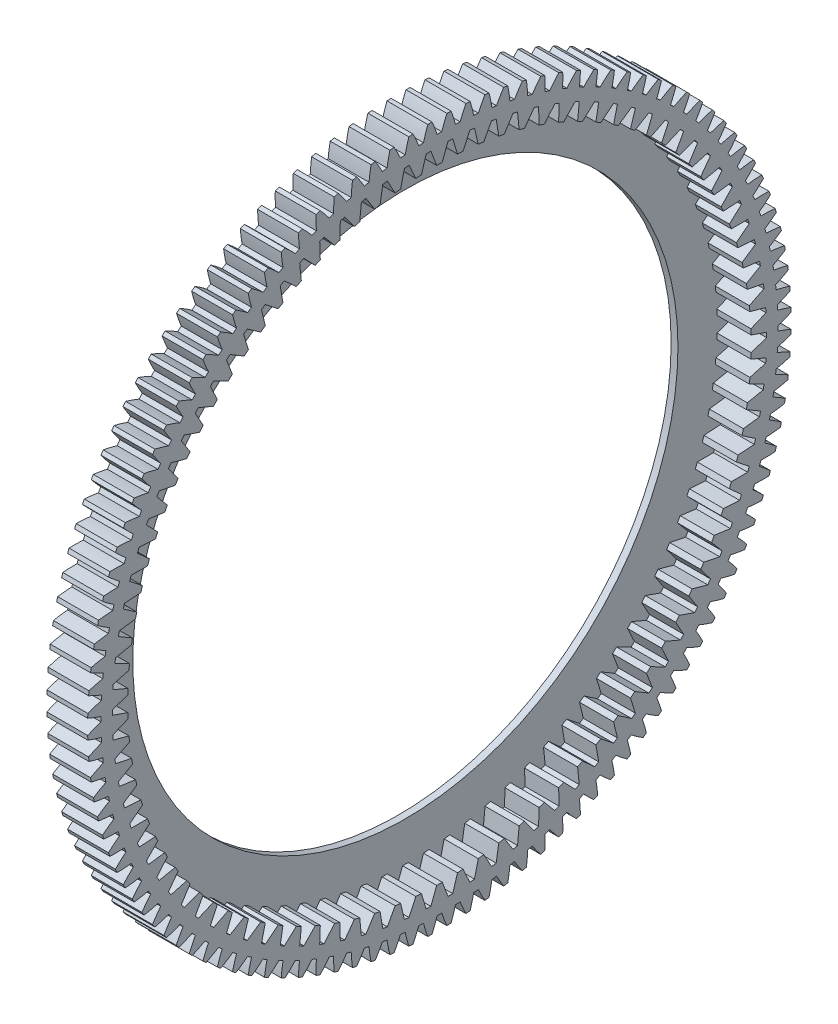
SolidWorks part; units mm, degrees
ref_plane "Plane1" through (0, 0, 0) normal (0, 0, 1) x (1, 0, 0)
ref_plane "Plane2" through (0, 0, 0) normal (0, 1, 0) x (1, 0, 0)
ref_plane "Plane3" through (0, 0, 0) normal (1, 0, 0) x (0, 0, -1)
sketch "HoldingSke" plane through (0, 0, 0) normal (0, 1, 0) x (1, 0, 0)
  line L0 (0, 0) -> (-0.2505, -0.5136)
  line L1 (-15, 0) -> (100, 0) construction
  line L2 (0, 0) -> (-2.1039, 2.3779)
  line L3 (0, 0) -> (-11.863, 4.5341)
  line L4 (0, 0) -> (-3.7858, 7.762)
  line L5 (0, 0) -> (-46.8476, -17.4728)
  line L6 (0, 0) -> (-9.9476, -6.7116)
  line L7 (-2.1039, 2.3779) -> (8.6586, 51.2059)
  line L8 (-76.2, 54.61) -> (-75.5, 54.61)
  line L9 (-71.009, 38.7566) -> (-53.1078, 45.2721)
  line L10 (-76.2, 71.12) -> (104.1128, 71.12)
  line L11 (0, 0) -> (-12, 0)
  line L12 (-76.2, 101.6) -> (-76.147, 101.6)
  line L13 (24.9733, 27.94) -> (52.9518, 28.4284)
  line L14 (24.9733, 27.94) -> (24.9743, 27.94)
  line L15 (24.9733, 27.94) -> (100.4006, 29.5858)
  line L16 (-63.627, -1.75) -> (-12.827, -1.75)
  circle A0 centre (0, 0) radius 2
  circle A1 centre (0, 0) radius 37.5
  circle A2 centre (0, 0) radius 37.5
  circle A3 centre (0, 0) radius 2
  dimension "MHD" = 75
  dimension "Hub_dia" = 75
  dimension "Bore" = 4
  dimension "MBD" = 4
  dimension "Num_teeth" = 116
  dimension "Pitch" = 0.5714
  dimension "Overall_len" = 50
  dimension "Show_teeth" = 116
  dimension "Thickness" = 12
  dimension "OAL" = 50.0001
  dimension "T_dim" = 0.7
  dimension "Ap" = 20
  dimension "H" = 19.05
  dimension "Pitch_radius" = 180.3128
  dimension "Width" = 12
  dimension "Backlash" = 0.053
  dimension "Addendum_fac" = 1
  dimension "Dedendum_fac" = 1.25
  dimension "Clearance_fac" = 0.25
  dimension "Dedendum_add" = 0.001
  dimension "Module" = 1.75
sketch "BasProSke" plane through (0, 0, 0) normal (0, 1, 0) x (1, 0, 0)
  line L0 (-10, 0) -> (60, 0) construction
  line L1 (0, 0) -> (0, 103.25)
  line L2 (0, 0) -> (12, 0)
  line L3 (12, 0) -> (12, 103.25)
  line L4 (12, 103.25) -> (0, 103.25)
  dimension "Thickness" = 12
  dimension "Diameter" = 206.5
revolve "Base-Revolve" add sketch "BasProSke" angle 360 about L0
sketch "TooCutSke" plane through (0, 0, 0) normal (1, 0, 0) x (0, 0, -1)
  line L1 (0, 0) -> (0, 107) construction
  line L2 (0, 0) -> (-1.4672, 101.4894) construction
  line L3 (0, 0) -> (-5.4967, 202.9094) construction
  line L4 (-1.4672, 101.4894) -> (-2.7483, 101.4547) construction
  arc A0 (0.6971, 99.3091) -> (-0.6971, 99.3091) centre (0, 0) ccw
  arc A1 (2.1948, 103.2521) -> (-2.1948, 103.2521) centre (0, 0) ccw
  circle A2 centre (0, 0) radius 101.5 construction
  circle A3 centre (0, 0) radius 95.3788 construction
  arc A4 (-0.6971, 99.3091) -> (-2.1948, 103.2521) centre (-39.349, 86.8837) ccw
  arc A5 (2.1948, 103.2521) -> (0.6971, 99.3091) centre (39.349, 86.8837) ccw
  dimension "Root_dia" = 198.623
  dimension "Overcut_dia" = 206.5508
  dimension "Pitch_dia" = 203
  dimension "Base_dia" = 190.7576
  dimension "Flank_rad" = 40.6
  dimension "Half_ang" = 1.552
  dimension "Half_CT" = 1.2817
extrude "ToothCut" cut sketch "TooCutSke" along normal through all
fillet "Breaks" [suppressed] radius 0.035
fillet "RootFillets" [suppressed] radius 0.4385
pattern_circular "TeethCuts" count 116 every 3.103 about axis through (-10, 0, 0) along (1, 0, 0) of "ToothCut", "RootFillets", "Breaks"
sketch "HubNeaOneSke" plane through (0, 0, 0) normal (-1, 0, 0) x (0, 0, 1)
  circle A0 centre (0, 0) radius 37.5
  dimension "Diameter" = 75
extrude "HubNearOne" [suppressed] add sketch "HubNeaOneSke" along normal blind 38.0001
sketch "HubNeaBotSke" plane through (0, 0, 0) normal (-1, 0, 0) x (0, 0, 1)
  circle A0 centre (0, 0) radius 37.5
  dimension "Diameter" = 75
extrude "HubNearBoth" [suppressed] add sketch "HubNeaBotSke" along normal blind 19
ref_plane "FarPln" through (12, 0, 0) normal (1, 0, 0) x (0, 0, -1)
sketch "HubFarSke" plane through (12, 0, 0) normal (1, 0, 0) x (0, 0, -1)
  circle A0 centre (0, 0) radius 37.5
  dimension "Diameter" = 75
extrude "HubFar" [suppressed] add sketch "HubFarSke" along normal blind 19
sketch "BorSke" plane through (0, 0, 0) normal (1, 0, 0) x (0, 0, -1)
  circle A0 centre (0, 0) radius 2
  dimension "Diameter" = 4
extrude "Bore" cut sketch "BorSke" along normal mid plane 100.0001
sketch "KeySke" plane through (0, 0, 0) normal (1, 0, 0) x (0, 0, -1)
  line L0 (-0.8, 0) -> (-0.8, 2.7)
  line L1 (-0.8, 2.7) -> (0.8, 2.7)
  line L2 (0.8, 2.7) -> (0.8, 0)
  line L3 (0, 0) -> (0, 34) construction
  line L4 (-0.8, 0) -> (0.8, 0)
  dimension "Offset" = 2.7
  dimension "Width" = 1.6
extrude "Keyway" [suppressed] cut sketch "KeySke" along normal mid plane 100.0001
pattern_circular "Keyway2" [suppressed] count 2 every 90 about axis through (-10, 0, 0) along (1, 0, 0)
sketch "Sketch1" plane through (12, 0, 0) normal (1, 0, 0) x (0, 0, -1)
  line L0 (3.8893, 95.9212) -> (5.2957, 91.3456)
  line L1 (2.5262, 95.9668) -> (0.8174, 91.4953)
  line L2 (8.9304, 95.5837) -> (6.9267, 91.2364)
  line L3 (10.2875, 95.4472) -> (11.3851, 90.7879)
  line L4 (15.2948, 94.7738) -> (13.0052, 90.57)
  line L5 (16.6397, 94.5469) -> (17.4236, 89.8247)
  line L6 (21.5908, 93.5406) -> (19.0256, 89.4991)
  line L7 (22.9175, 93.2244) -> (23.3843, 88.4604)
  line L8 (27.7904, 91.8896) -> (24.961, 88.0285)
  line L9 (29.0931, 91.4855) -> (29.2406, 86.7009)
  line L10 (33.8659, 89.8282) -> (30.7849, 86.1647)
  line L11 (35.1387, 89.338) -> (34.9663, 84.5543)
  line L12 (39.7901, 87.3656) -> (36.4713, 83.9161)
  line L13 (41.0273, 86.7915) -> (40.5358, 82.03)
  line L14 (45.5366, 84.5128) -> (41.9948, 81.2927)
  line L15 (46.7327, 83.8573) -> (45.9243, 79.1393)
  line L16 (51.0798, 81.2826) -> (47.3308, 78.3062)
  line L17 (52.2294, 80.5487) -> (51.1077, 75.8951)
  line L18 (56.3948, 77.6893) -> (52.4554, 74.97)
  line L19 (57.4928, 76.8803) -> (56.0628, 72.3121)
  line L20 (61.4579, 73.749) -> (57.3457, 71.2989)
  line L21 (62.4995, 72.8685) -> (60.7675, 68.406)
  line L22 (66.2466, 69.4794) -> (61.9799, 67.3094)
  line L23 (67.227, 68.5312) -> (65.2008, 64.1944)
  line L24 (70.7394, 64.8995) -> (66.3372, 63.0193)
  line L25 (71.6542, 63.8879) -> (69.3429, 59.6961)
  line L26 (74.9162, 60.0297) -> (70.3983, 58.4478)
  line L27 (75.7615, 58.9593) -> (73.1753, 54.9312)
  line L28 (78.7584, 54.8918) -> (74.145, 53.6152)
  line L29 (79.5303, 53.7673) -> (76.6809, 49.921)
  line L30 (82.2489, 49.5087) -> (77.5605, 48.5431)
  line L31 (82.944, 48.3352) -> (79.844, 44.6878)
  line L32 (85.3721, 43.9045) -> (80.6296, 43.2542)
  line L33 (85.9872, 42.6872) -> (82.6505, 39.255)
  line L34 (88.1139, 38.1043) -> (83.3387, 37.7722)
  line L35 (88.6464, 36.8486) -> (85.0879, 33.6469)
  line L36 (90.4622, 32.1338) -> (85.6755, 32.1214)
  line L37 (90.9096, 30.8454) -> (87.1453, 27.8885)
  line L38 (92.4065, 26.0198) -> (87.6296, 26.3272)
  line L39 (92.7669, 24.7044) -> (88.8134, 22.0056)
  line L40 (93.9381, 19.7897) -> (89.1924, 20.4154)
  line L41 (94.2098, 18.4531) -> (90.0849, 16.0243)
  line L42 (95.0501, 13.4711) -> (90.3568, 14.4124)
  line L43 (95.2319, 12.1194) -> (90.954, 9.9715)
  line L44 (95.7377, 7.0924) -> (91.1177, 8.345)
  line L45 (95.8288, 5.7315) -> (91.4169, 3.8742)
  line L46 (95.9976, 0.682) -> (91.4716, 2.2404)
  line L47 (95.9976, -0.682) -> (91.4716, -2.2404)
  line L48 (95.8288, -5.7315) -> (91.4169, -3.8742)
  line L49 (95.7377, -7.0924) -> (91.1177, -8.345)
  line L50 (95.2319, -12.1194) -> (90.954, -9.9715)
  line L51 (95.0501, -13.4711) -> (90.3568, -14.4124)
  line L52 (94.2098, -18.4531) -> (90.0849, -16.0243)
  line L53 (93.9381, -19.7897) -> (89.1924, -20.4154)
  line L54 (92.7669, -24.7044) -> (88.8134, -22.0056)
  line L55 (92.4065, -26.0198) -> (87.6296, -26.3272)
  line L56 (90.9096, -30.8454) -> (87.1453, -27.8885)
  line L57 (90.4622, -32.1338) -> (85.6755, -32.1214)
  line L58 (88.6464, -36.8486) -> (85.0879, -33.6469)
  line L59 (88.1139, -38.1043) -> (83.3387, -37.7722)
  line L60 (85.9872, -42.6872) -> (82.6505, -39.255)
  line L61 (85.3721, -43.9045) -> (80.6296, -43.2542)
  line L62 (82.944, -48.3352) -> (79.844, -44.6878)
  line L63 (82.2489, -49.5087) -> (77.5605, -48.5431)
  line L64 (79.5303, -53.7673) -> (76.6809, -49.921)
  line L65 (78.7584, -54.8918) -> (74.145, -53.6152)
  line L66 (75.7615, -58.9593) -> (73.1753, -54.9312)
  line L67 (74.9162, -60.0297) -> (70.3983, -58.4478)
  line L68 (71.6542, -63.8879) -> (69.3429, -59.6961)
  line L69 (70.7394, -64.8995) -> (66.3372, -63.0193)
  line L70 (67.227, -68.5312) -> (65.2008, -64.1944)
  line L71 (66.2466, -69.4794) -> (61.9799, -67.3094)
  line L72 (62.4995, -72.8685) -> (60.7675, -68.406)
  line L73 (61.4579, -73.749) -> (57.3457, -71.2989)
  line L74 (57.4928, -76.8803) -> (56.0628, -72.3121)
  line L75 (56.3948, -77.6893) -> (52.4554, -74.97)
  line L76 (52.2294, -80.5487) -> (51.1077, -75.8951)
  line L77 (51.0798, -81.2826) -> (47.3308, -78.3062)
  line L78 (46.7327, -83.8573) -> (45.9243, -79.1393)
  line L79 (45.5366, -84.5128) -> (41.9948, -81.2927)
  line L80 (41.0273, -86.7915) -> (40.5358, -82.03)
  line L81 (39.7901, -87.3656) -> (36.4713, -83.9161)
  line L82 (35.1387, -89.338) -> (34.9663, -84.5543)
  line L83 (33.8659, -89.8282) -> (30.7849, -86.1647)
  line L84 (29.0931, -91.4855) -> (29.2406, -86.7009)
  line L85 (27.7904, -91.8896) -> (24.961, -88.0285)
  line L86 (22.9175, -93.2244) -> (23.3843, -88.4604)
  line L87 (21.5908, -93.5406) -> (19.0256, -89.4991)
  line L88 (16.6397, -94.5469) -> (17.4236, -89.8247)
  line L89 (15.2948, -94.7738) -> (13.0052, -90.57)
  line L90 (10.2875, -95.4472) -> (11.3851, -90.7879)
  line L91 (8.9304, -95.5837) -> (6.9267, -91.2364)
  line L92 (3.8893, -95.9212) -> (5.2957, -91.3456)
  line L93 (2.5262, -95.9668) -> (0.8174, -91.4953)
  line L94 (-2.5262, -95.9668) -> (-0.8174, -91.4953)
  line L95 (-3.8893, -95.9212) -> (-5.2957, -91.3456)
  line L96 (-8.9304, -95.5837) -> (-6.9267, -91.2364)
  line L97 (-10.2875, -95.4472) -> (-11.3851, -90.7879)
  line L98 (-15.2948, -94.7738) -> (-13.0052, -90.57)
  line L99 (-16.6397, -94.5469) -> (-17.4236, -89.8247)
  line L100 (-21.5908, -93.5406) -> (-19.0256, -89.4991)
  line L101 (-22.9175, -93.2244) -> (-23.3843, -88.4604)
  line L102 (-27.7904, -91.8896) -> (-24.961, -88.0285)
  line L103 (-29.0931, -91.4855) -> (-29.2406, -86.7009)
  line L104 (-33.8659, -89.8282) -> (-30.7849, -86.1647)
  line L105 (-35.1387, -89.338) -> (-34.9663, -84.5543)
  line L106 (-39.7901, -87.3656) -> (-36.4713, -83.9161)
  line L107 (-41.0273, -86.7915) -> (-40.5358, -82.03)
  line L108 (-45.5366, -84.5128) -> (-41.9948, -81.2927)
  line L109 (-46.7327, -83.8573) -> (-45.9243, -79.1393)
  line L110 (-51.0798, -81.2826) -> (-47.3308, -78.3062)
  line L111 (-52.2294, -80.5487) -> (-51.1077, -75.8951)
  line L112 (-56.3948, -77.6893) -> (-52.4554, -74.97)
  line L113 (-57.4928, -76.8803) -> (-56.0628, -72.3121)
  line L114 (-61.4579, -73.749) -> (-57.3457, -71.2989)
  line L115 (-62.4995, -72.8685) -> (-60.7675, -68.406)
  line L116 (-66.2466, -69.4794) -> (-61.9799, -67.3094)
  line L117 (-67.227, -68.5312) -> (-65.2008, -64.1944)
  line L118 (-70.7394, -64.8995) -> (-66.3372, -63.0193)
  line L119 (-71.6542, -63.8879) -> (-69.3429, -59.6961)
  line L120 (-74.9162, -60.0297) -> (-70.3983, -58.4478)
  line L121 (-75.7615, -58.9593) -> (-73.1753, -54.9312)
  line L122 (-78.7584, -54.8918) -> (-74.145, -53.6152)
  line L123 (-79.5303, -53.7673) -> (-76.6809, -49.921)
  line L124 (-82.2489, -49.5087) -> (-77.5605, -48.5431)
  line L125 (-82.944, -48.3352) -> (-79.844, -44.6878)
  line L126 (-85.3721, -43.9045) -> (-80.6296, -43.2542)
  line L127 (-85.9872, -42.6872) -> (-82.6505, -39.255)
  line L128 (-88.1139, -38.1043) -> (-83.3387, -37.7722)
  line L129 (-88.6464, -36.8486) -> (-85.0879, -33.6469)
  line L130 (-90.4622, -32.1338) -> (-85.6755, -32.1214)
  line L131 (-90.9096, -30.8454) -> (-87.1453, -27.8885)
  line L132 (-92.4065, -26.0198) -> (-87.6296, -26.3272)
  line L133 (-92.7669, -24.7044) -> (-88.8134, -22.0056)
  line L134 (-93.9381, -19.7897) -> (-89.1924, -20.4154)
  line L135 (-94.2098, -18.4531) -> (-90.0849, -16.0243)
  line L136 (-95.0501, -13.4711) -> (-90.3568, -14.4124)
  line L137 (-95.2319, -12.1194) -> (-90.954, -9.9715)
  line L138 (-95.7377, -7.0924) -> (-91.1177, -8.345)
  line L139 (-95.8288, -5.7315) -> (-91.4169, -3.8742)
  line L140 (-95.9976, -0.682) -> (-91.4716, -2.2404)
  line L141 (-95.9976, 0.682) -> (-91.4716, 2.2404)
  line L142 (-95.8288, 5.7315) -> (-91.4169, 3.8742)
  line L143 (-95.7377, 7.0924) -> (-91.1177, 8.345)
  line L144 (-95.2319, 12.1194) -> (-90.954, 9.9715)
  line L145 (-95.0501, 13.4711) -> (-90.3568, 14.4124)
  line L146 (-94.2098, 18.4531) -> (-90.0849, 16.0243)
  line L147 (-93.9381, 19.7897) -> (-89.1924, 20.4154)
  line L148 (-92.7669, 24.7044) -> (-88.8134, 22.0056)
  line L149 (-92.4065, 26.0198) -> (-87.6296, 26.3272)
  line L150 (-90.9096, 30.8454) -> (-87.1453, 27.8885)
  line L151 (-90.4622, 32.1338) -> (-85.6755, 32.1214)
  line L152 (-88.6464, 36.8486) -> (-85.0879, 33.6469)
  line L153 (-88.1139, 38.1043) -> (-83.3387, 37.7722)
  line L154 (-85.9872, 42.6872) -> (-82.6505, 39.255)
  line L155 (-85.3721, 43.9045) -> (-80.6296, 43.2542)
  line L156 (-82.944, 48.3352) -> (-79.844, 44.6878)
  line L157 (-82.2489, 49.5087) -> (-77.5605, 48.5431)
  line L158 (-79.5303, 53.7673) -> (-76.6809, 49.921)
  line L159 (-78.7584, 54.8918) -> (-74.145, 53.6152)
  line L160 (-75.7615, 58.9593) -> (-73.1753, 54.9312)
  line L161 (-74.9162, 60.0297) -> (-70.3983, 58.4478)
  line L162 (-71.6542, 63.8879) -> (-69.3429, 59.6961)
  line L163 (-70.7394, 64.8995) -> (-66.3372, 63.0193)
  line L164 (-67.227, 68.5312) -> (-65.2008, 64.1944)
  line L165 (-66.2466, 69.4794) -> (-61.9799, 67.3094)
  line L166 (-62.4995, 72.8685) -> (-60.7675, 68.406)
  line L167 (-61.4579, 73.749) -> (-57.3457, 71.2989)
  line L168 (-57.4928, 76.8803) -> (-56.0628, 72.3121)
  line L169 (-56.3948, 77.6893) -> (-52.4554, 74.97)
  line L170 (-52.2294, 80.5487) -> (-51.1077, 75.8951)
  line L171 (-51.0798, 81.2826) -> (-47.3308, 78.3062)
  line L172 (-46.7327, 83.8573) -> (-45.9243, 79.1393)
  line L173 (-45.5366, 84.5128) -> (-41.9948, 81.2927)
  line L174 (-41.0273, 86.7915) -> (-40.5358, 82.03)
  line L175 (-39.7901, 87.3656) -> (-36.4713, 83.9161)
  line L176 (-35.1387, 89.338) -> (-34.9663, 84.5543)
  line L177 (-33.8659, 89.8282) -> (-30.7849, 86.1647)
  line L178 (-29.0931, 91.4855) -> (-29.2406, 86.7009)
  line L179 (-27.7904, 91.8896) -> (-24.961, 88.0285)
  line L180 (-22.9175, 93.2244) -> (-23.3843, 88.4604)
  line L181 (-21.5908, 93.5406) -> (-19.0256, 89.4991)
  line L182 (-16.6397, 94.5469) -> (-17.4236, 89.8247)
  line L183 (-15.2948, 94.7738) -> (-13.0052, 90.57)
  line L184 (-10.2875, 95.4472) -> (-11.3851, 90.7879)
  line L185 (-8.9304, 95.5837) -> (-6.9267, 91.2364)
  line L186 (-3.8893, 95.9212) -> (-5.2957, 91.3456)
  line L187 (-2.5262, 95.9668) -> (-0.8174, 91.4953)
  arc A0 (3.8893, 95.9212) -> (2.5262, 95.9668) centre (0, 0) ccw
  circle A1 centre (0, 0) radius 96 construction
  arc A2 (10.2875, 95.4472) -> (8.9304, 95.5837) centre (0, 0) ccw
  arc A3 (16.6397, 94.5469) -> (15.2948, 94.7738) centre (0, 0) ccw
  arc A4 (22.9175, 93.2244) -> (21.5908, 93.5406) centre (0, 0) ccw
  arc A5 (29.0931, 91.4855) -> (27.7904, 91.8896) centre (0, 0) ccw
  arc A6 (35.1387, 89.338) -> (33.8659, 89.8282) centre (0, 0) ccw
  arc A7 (41.0273, 86.7915) -> (39.7901, 87.3656) centre (0, 0) ccw
  arc A8 (46.7327, 83.8573) -> (45.5366, 84.5128) centre (0, 0) ccw
  arc A9 (52.2294, 80.5487) -> (51.0798, 81.2826) centre (0, 0) ccw
  arc A10 (57.4928, 76.8803) -> (56.3948, 77.6893) centre (0, 0) ccw
  arc A11 (62.4995, 72.8685) -> (61.4579, 73.749) centre (0, 0) ccw
  arc A12 (67.227, 68.5312) -> (66.2466, 69.4794) centre (0, 0) ccw
  arc A13 (71.6542, 63.8879) -> (70.7394, 64.8995) centre (0, 0) ccw
  arc A14 (75.7615, 58.9593) -> (74.9162, 60.0297) centre (0, 0) ccw
  arc A15 (79.5303, 53.7673) -> (78.7584, 54.8918) centre (0, 0) ccw
  arc A16 (82.944, 48.3352) -> (82.2489, 49.5087) centre (0, 0) ccw
  arc A17 (85.9872, 42.6872) -> (85.3721, 43.9045) centre (0, 0) ccw
  arc A18 (88.6464, 36.8486) -> (88.1139, 38.1043) centre (0, 0) ccw
  arc A19 (90.9096, 30.8454) -> (90.4622, 32.1338) centre (0, 0) ccw
  arc A20 (92.7669, 24.7044) -> (92.4065, 26.0198) centre (0, 0) ccw
  arc A21 (94.2098, 18.4531) -> (93.9381, 19.7897) centre (0, 0) ccw
  arc A22 (95.2319, 12.1194) -> (95.0501, 13.4711) centre (0, 0) ccw
  arc A23 (95.8288, 5.7315) -> (95.7377, 7.0924) centre (0, 0) ccw
  arc A24 (95.9976, -0.682) -> (95.9976, 0.682) centre (0, 0) ccw
  arc A25 (95.7377, -7.0924) -> (95.8288, -5.7315) centre (0, 0) ccw
  arc A26 (95.0501, -13.4711) -> (95.2319, -12.1194) centre (0, 0) ccw
  arc A27 (93.9381, -19.7897) -> (94.2098, -18.4531) centre (0, 0) ccw
  arc A28 (92.4065, -26.0198) -> (92.7669, -24.7044) centre (0, 0) ccw
  arc A29 (90.4622, -32.1338) -> (90.9096, -30.8454) centre (0, 0) ccw
  arc A30 (88.1139, -38.1043) -> (88.6464, -36.8486) centre (0, 0) ccw
  arc A31 (85.3721, -43.9045) -> (85.9872, -42.6872) centre (0, 0) ccw
  arc A32 (82.2489, -49.5087) -> (82.944, -48.3352) centre (0, 0) ccw
  arc A33 (78.7584, -54.8918) -> (79.5303, -53.7673) centre (0, 0) ccw
  arc A34 (74.9162, -60.0297) -> (75.7615, -58.9593) centre (0, 0) ccw
  arc A35 (70.7394, -64.8995) -> (71.6542, -63.8879) centre (0, 0) ccw
  arc A36 (66.2466, -69.4794) -> (67.227, -68.5312) centre (0, 0) ccw
  arc A37 (61.4579, -73.749) -> (62.4995, -72.8685) centre (0, 0) ccw
  arc A38 (56.3948, -77.6893) -> (57.4928, -76.8803) centre (0, 0) ccw
  arc A39 (51.0798, -81.2826) -> (52.2294, -80.5487) centre (0, 0) ccw
  arc A40 (45.5366, -84.5128) -> (46.7327, -83.8573) centre (0, 0) ccw
  arc A41 (39.7901, -87.3656) -> (41.0273, -86.7915) centre (0, 0) ccw
  arc A42 (33.8659, -89.8282) -> (35.1387, -89.338) centre (0, 0) ccw
  arc A43 (27.7904, -91.8896) -> (29.0931, -91.4855) centre (0, 0) ccw
  arc A44 (21.5908, -93.5406) -> (22.9175, -93.2244) centre (0, 0) ccw
  arc A45 (15.2948, -94.7738) -> (16.6397, -94.5469) centre (0, 0) ccw
  arc A46 (8.9304, -95.5837) -> (10.2875, -95.4472) centre (0, 0) ccw
  arc A47 (2.5262, -95.9668) -> (3.8893, -95.9212) centre (0, 0) ccw
  arc A48 (-3.8893, -95.9212) -> (-2.5262, -95.9668) centre (0, 0) ccw
  arc A49 (-10.2875, -95.4472) -> (-8.9304, -95.5837) centre (0, 0) ccw
  arc A50 (-16.6397, -94.5469) -> (-15.2948, -94.7738) centre (0, 0) ccw
  arc A51 (-22.9175, -93.2244) -> (-21.5908, -93.5406) centre (0, 0) ccw
  arc A52 (-29.0931, -91.4855) -> (-27.7904, -91.8896) centre (0, 0) ccw
  arc A53 (-35.1387, -89.338) -> (-33.8659, -89.8282) centre (0, 0) ccw
  arc A54 (-41.0273, -86.7915) -> (-39.7901, -87.3656) centre (0, 0) ccw
  arc A55 (-46.7327, -83.8573) -> (-45.5366, -84.5128) centre (0, 0) ccw
  arc A56 (-52.2294, -80.5487) -> (-51.0798, -81.2826) centre (0, 0) ccw
  arc A57 (-57.4928, -76.8803) -> (-56.3948, -77.6893) centre (0, 0) ccw
  arc A58 (-62.4995, -72.8685) -> (-61.4579, -73.749) centre (0, 0) ccw
  arc A59 (-67.227, -68.5312) -> (-66.2466, -69.4794) centre (0, 0) ccw
  arc A60 (-71.6542, -63.8879) -> (-70.7394, -64.8995) centre (0, 0) ccw
  arc A61 (-75.7615, -58.9593) -> (-74.9162, -60.0297) centre (0, 0) ccw
  arc A62 (-79.5303, -53.7673) -> (-78.7584, -54.8918) centre (0, 0) ccw
  arc A63 (-82.944, -48.3352) -> (-82.2489, -49.5087) centre (0, 0) ccw
  arc A64 (-85.9872, -42.6872) -> (-85.3721, -43.9045) centre (0, 0) ccw
  arc A65 (-88.6464, -36.8486) -> (-88.1139, -38.1043) centre (0, 0) ccw
  arc A66 (-90.9096, -30.8454) -> (-90.4622, -32.1338) centre (0, 0) ccw
  arc A67 (-92.7669, -24.7044) -> (-92.4065, -26.0198) centre (0, 0) ccw
  arc A68 (-94.2098, -18.4531) -> (-93.9381, -19.7897) centre (0, 0) ccw
  arc A69 (-95.2319, -12.1194) -> (-95.0501, -13.4711) centre (0, 0) ccw
  arc A70 (-95.8288, -5.7315) -> (-95.7377, -7.0924) centre (0, 0) ccw
  arc A71 (-95.9976, 0.682) -> (-95.9976, -0.682) centre (0, 0) ccw
  arc A72 (-95.7377, 7.0924) -> (-95.8288, 5.7315) centre (0, 0) ccw
  arc A73 (-95.0501, 13.4711) -> (-95.2319, 12.1194) centre (0, 0) ccw
  arc A74 (-93.9381, 19.7897) -> (-94.2098, 18.4531) centre (0, 0) ccw
  arc A75 (-92.4065, 26.0198) -> (-92.7669, 24.7044) centre (0, 0) ccw
  arc A76 (-90.4622, 32.1338) -> (-90.9096, 30.8454) centre (0, 0) ccw
  arc A77 (-88.1139, 38.1043) -> (-88.6464, 36.8486) centre (0, 0) ccw
  arc A78 (-85.3721, 43.9045) -> (-85.9872, 42.6872) centre (0, 0) ccw
  arc A79 (-82.2489, 49.5087) -> (-82.944, 48.3352) centre (0, 0) ccw
  arc A80 (-78.7584, 54.8918) -> (-79.5303, 53.7673) centre (0, 0) ccw
  arc A81 (-74.9162, 60.0297) -> (-75.7615, 58.9593) centre (0, 0) ccw
  arc A82 (-70.7394, 64.8995) -> (-71.6542, 63.8879) centre (0, 0) ccw
  arc A83 (-66.2466, 69.4794) -> (-67.227, 68.5312) centre (0, 0) ccw
  arc A84 (-61.4579, 73.749) -> (-62.4995, 72.8685) centre (0, 0) ccw
  arc A85 (-56.3948, 77.6893) -> (-57.4928, 76.8803) centre (0, 0) ccw
  arc A86 (-51.0798, 81.2826) -> (-52.2294, 80.5487) centre (0, 0) ccw
  arc A87 (-45.5366, 84.5128) -> (-46.7327, 83.8573) centre (0, 0) ccw
  arc A88 (-39.7901, 87.3656) -> (-41.0273, 86.7915) centre (0, 0) ccw
  arc A89 (-33.8659, 89.8282) -> (-35.1387, 89.338) centre (0, 0) ccw
  arc A90 (-27.7904, 91.8896) -> (-29.0931, 91.4855) centre (0, 0) ccw
  arc A91 (-21.5908, 93.5406) -> (-22.9175, 93.2244) centre (0, 0) ccw
  arc A92 (-15.2948, 94.7738) -> (-16.6397, 94.5469) centre (0, 0) ccw
  arc A93 (-8.9304, 95.5837) -> (-10.2875, 95.4472) centre (0, 0) ccw
  arc A94 (-2.5262, 95.9668) -> (-3.8893, 95.9212) centre (0, 0) ccw
  arc A95 (-5.2957, 91.3456) -> (-6.9267, 91.2364) centre (0, 0) ccw
  arc A96 (-11.3851, 90.7879) -> (-13.0052, 90.57) centre (0, 0) ccw
  arc A97 (0.8174, 91.4953) -> (-0.8174, 91.4953) centre (0, 0) ccw
  arc A98 (6.9267, 91.2364) -> (5.2957, 91.3456) centre (0, 0) ccw
  arc A99 (-17.4236, 89.8247) -> (-19.0256, 89.4991) centre (0, 0) ccw
  arc A100 (13.0052, 90.57) -> (11.3851, 90.7879) centre (0, 0) ccw
  arc A101 (19.0256, 89.4991) -> (17.4236, 89.8247) centre (0, 0) ccw
  arc A102 (24.961, 88.0285) -> (23.3843, 88.4604) centre (0, 0) ccw
  arc A103 (30.7849, 86.1647) -> (29.2406, 86.7009) centre (0, 0) ccw
  arc A104 (36.4713, 83.9161) -> (34.9663, 84.5543) centre (0, 0) ccw
  arc A105 (41.9948, 81.2927) -> (40.5358, 82.03) centre (0, 0) ccw
  arc A106 (47.3308, 78.3062) -> (45.9243, 79.1393) centre (0, 0) ccw
  arc A107 (52.4554, 74.97) -> (51.1077, 75.8951) centre (0, 0) ccw
  arc A108 (-23.3843, 88.4604) -> (-24.961, 88.0285) centre (0, 0) ccw
  arc A109 (-29.2406, 86.7009) -> (-30.7849, 86.1647) centre (0, 0) ccw
  arc A110 (-34.9663, 84.5543) -> (-36.4713, 83.9161) centre (0, 0) ccw
  arc A111 (-40.5358, 82.03) -> (-41.9948, 81.2927) centre (0, 0) ccw
  arc A112 (-45.9243, 79.1393) -> (-47.3308, 78.3062) centre (0, 0) ccw
  arc A113 (-51.1077, 75.8951) -> (-52.4554, 74.97) centre (0, 0) ccw
  arc A114 (-56.0628, 72.3121) -> (-57.3457, 71.2989) centre (0, 0) ccw
  arc A115 (-60.7675, 68.406) -> (-61.9799, 67.3094) centre (0, 0) ccw
  arc A116 (-65.2008, 64.1944) -> (-66.3372, 63.0193) centre (0, 0) ccw
  arc A117 (-69.3429, 59.6961) -> (-70.3983, 58.4478) centre (0, 0) ccw
  arc A118 (-73.1753, 54.9312) -> (-74.145, 53.6152) centre (0, 0) ccw
  arc A119 (-76.6809, 49.921) -> (-77.5605, 48.5431) centre (0, 0) ccw
  arc A120 (-79.844, 44.6878) -> (-80.6296, 43.2542) centre (0, 0) ccw
  arc A121 (-82.6505, 39.255) -> (-83.3387, 37.7722) centre (0, 0) ccw
  arc A122 (-85.0879, 33.6469) -> (-85.6755, 32.1214) centre (0, 0) ccw
  arc A123 (-87.1453, 27.8885) -> (-87.6296, 26.3272) centre (0, 0) ccw
  arc A124 (-88.8134, 22.0056) -> (-89.1924, 20.4154) centre (0, 0) ccw
  arc A125 (-90.0849, 16.0243) -> (-90.3568, 14.4124) centre (0, 0) ccw
  arc A126 (-90.954, 9.9715) -> (-91.1177, 8.345) centre (0, 0) ccw
  arc A127 (-91.4169, 3.8742) -> (-91.4716, 2.2404) centre (0, 0) ccw
  arc A128 (-91.4716, -2.2404) -> (-91.4169, -3.8742) centre (0, 0) ccw
  arc A129 (-91.1177, -8.345) -> (-90.954, -9.9715) centre (0, 0) ccw
  arc A130 (-90.3568, -14.4124) -> (-90.0849, -16.0243) centre (0, 0) ccw
  arc A131 (-89.1924, -20.4154) -> (-88.8134, -22.0056) centre (0, 0) ccw
  arc A132 (-87.6296, -26.3272) -> (-87.1453, -27.8885) centre (0, 0) ccw
  arc A133 (-85.6755, -32.1214) -> (-85.0879, -33.6469) centre (0, 0) ccw
  arc A134 (-83.3387, -37.7722) -> (-82.6505, -39.255) centre (0, 0) ccw
  arc A135 (-80.6296, -43.2542) -> (-79.844, -44.6878) centre (0, 0) ccw
  arc A136 (-77.5605, -48.5431) -> (-76.6809, -49.921) centre (0, 0) ccw
  arc A137 (-74.145, -53.6152) -> (-73.1753, -54.9312) centre (0, 0) ccw
  arc A138 (57.3457, 71.2989) -> (56.0628, 72.3121) centre (0, 0) ccw
  arc A139 (61.9799, 67.3094) -> (60.7675, 68.406) centre (0, 0) ccw
  arc A140 (66.3372, 63.0193) -> (65.2008, 64.1944) centre (0, 0) ccw
  arc A141 (70.3983, 58.4478) -> (69.3429, 59.6961) centre (0, 0) ccw
  arc A142 (74.145, 53.6152) -> (73.1753, 54.9312) centre (0, 0) ccw
  arc A143 (77.5605, 48.5431) -> (76.6809, 49.921) centre (0, 0) ccw
  arc A144 (80.6296, 43.2542) -> (79.844, 44.6878) centre (0, 0) ccw
  arc A145 (83.3387, 37.7722) -> (82.6505, 39.255) centre (0, 0) ccw
  arc A146 (85.6755, 32.1214) -> (85.0879, 33.6469) centre (0, 0) ccw
  arc A147 (87.6296, 26.3272) -> (87.1453, 27.8885) centre (0, 0) ccw
  arc A148 (89.1924, 20.4154) -> (88.8134, 22.0056) centre (0, 0) ccw
  arc A149 (90.3568, 14.4124) -> (90.0849, 16.0243) centre (0, 0) ccw
  arc A150 (91.1177, 8.345) -> (90.954, 9.9715) centre (0, 0) ccw
  arc A151 (91.4716, 2.2404) -> (91.4169, 3.8742) centre (0, 0) ccw
  arc A152 (91.4169, -3.8742) -> (91.4716, -2.2404) centre (0, 0) ccw
  arc A153 (90.954, -9.9715) -> (91.1177, -8.345) centre (0, 0) ccw
  arc A154 (90.0849, -16.0243) -> (90.3568, -14.4124) centre (0, 0) ccw
  arc A155 (88.8134, -22.0056) -> (89.1924, -20.4154) centre (0, 0) ccw
  arc A156 (87.1453, -27.8885) -> (87.6296, -26.3272) centre (0, 0) ccw
  arc A157 (85.0879, -33.6469) -> (85.6755, -32.1214) centre (0, 0) ccw
  arc A158 (82.6505, -39.255) -> (83.3387, -37.7722) centre (0, 0) ccw
  arc A159 (79.844, -44.6878) -> (80.6296, -43.2542) centre (0, 0) ccw
  arc A160 (76.6809, -49.921) -> (77.5605, -48.5431) centre (0, 0) ccw
  arc A161 (73.1753, -54.9312) -> (74.145, -53.6152) centre (0, 0) ccw
  arc A162 (69.3429, -59.6961) -> (70.3983, -58.4478) centre (0, 0) ccw
  arc A163 (65.2008, -64.1944) -> (66.3372, -63.0193) centre (0, 0) ccw
  arc A164 (60.7675, -68.406) -> (61.9799, -67.3094) centre (0, 0) ccw
  arc A165 (56.0628, -72.3121) -> (57.3457, -71.2989) centre (0, 0) ccw
  arc A166 (51.1077, -75.8951) -> (52.4554, -74.97) centre (0, 0) ccw
  arc A167 (45.9243, -79.1393) -> (47.3308, -78.3062) centre (0, 0) ccw
  arc A168 (40.5358, -82.03) -> (41.9948, -81.2927) centre (0, 0) ccw
  arc A169 (34.9663, -84.5543) -> (36.4713, -83.9161) centre (0, 0) ccw
  arc A170 (29.2406, -86.7009) -> (30.7849, -86.1647) centre (0, 0) ccw
  arc A171 (23.3843, -88.4604) -> (24.961, -88.0285) centre (0, 0) ccw
  arc A172 (17.4236, -89.8247) -> (19.0256, -89.4991) centre (0, 0) ccw
  arc A173 (11.3851, -90.7879) -> (13.0052, -90.57) centre (0, 0) ccw
  arc A174 (5.2957, -91.3456) -> (6.9267, -91.2364) centre (0, 0) ccw
  arc A175 (-0.8174, -91.4953) -> (0.8174, -91.4953) centre (0, 0) ccw
  arc A176 (-6.9267, -91.2364) -> (-5.2957, -91.3456) centre (0, 0) ccw
  arc A177 (-13.0052, -90.57) -> (-11.3851, -90.7879) centre (0, 0) ccw
  arc A178 (-19.0256, -89.4991) -> (-17.4236, -89.8247) centre (0, 0) ccw
  arc A179 (-24.961, -88.0285) -> (-23.3843, -88.4604) centre (0, 0) ccw
  arc A180 (-30.7849, -86.1647) -> (-29.2406, -86.7009) centre (0, 0) ccw
  arc A181 (-36.4713, -83.9161) -> (-34.9663, -84.5543) centre (0, 0) ccw
  arc A182 (-41.9948, -81.2927) -> (-40.5358, -82.03) centre (0, 0) ccw
  arc A183 (-47.3308, -78.3062) -> (-45.9243, -79.1393) centre (0, 0) ccw
  arc A184 (-52.4554, -74.97) -> (-51.1077, -75.8951) centre (0, 0) ccw
  arc A185 (-57.3457, -71.2989) -> (-56.0628, -72.3121) centre (0, 0) ccw
  arc A186 (-61.9799, -67.3094) -> (-60.7675, -68.406) centre (0, 0) ccw
  arc A187 (-66.3372, -63.0193) -> (-65.2008, -64.1944) centre (0, 0) ccw
  arc A188 (-70.3983, -58.4478) -> (-69.3429, -59.6961) centre (0, 0) ccw
  point P0 (0, 0)
  point P380 (0, 0)
  dimension "D1" = 192
extrude "Cut-Extrude1" cut sketch "Sketch1" against normal blind 10
sketch "Sketch2" plane through (2, 0, 0) normal (1, 0, 0) x (0, 0, -1)
  circle A0 centre (0, 0) radius 80
  circle A2 centre (0, 0) radius 96 construction
  point P2 (0, 0)
  point P5 (-1.5896, 1.2137)
  dimension "D1" = 192
  dimension "D2" = 160
extrude "Cut-Extrude2" cut sketch "Sketch2" against normal blind 10
equation "' \"Module@HoldingSke\" = 6.35"
equation "' \"Num_teeth@HoldingSke\" = 12"
equation "' \"Ap@HoldingSke\" =  20"
equation "' \"Ap@HoldingSke\" = 20"
equation "' \"Width@HoldingSke\" = 0.5 * 25.4"
equation "' \"Hub_dia@HoldingSke\"= 1 * 25.4"
equation "' \"Hub_dia@HoldingSke\" = 1 * 25.4"
equation "' \"Overall_len@HoldingSke\" = 1.0 * 25.4"
equation "' \"Bore@HoldingSke\" = 0.75 * 25.4"
equation "' \"T_dim@HoldingSke\" = 0.1 * 25.4"
equation "' \"Width@KeySke\" = 0.25 * 25.4"
equation "' \"Show_teeth@HoldingSke\" = 13"
equation "' \"Backlash@HoldingSke\" = 0.009 * 25.4"
equation "' \"Addendum_fac@HoldingSke\" = 1.0"
equation "' \"Dedendum_fac@HoldingSke\" = 1.25"
equation "' \"Dedendum_add@HoldingSke\" = 0.00005 * 25.4"
equation "' \"Clearance_fac@HoldingSke\" = 0.25"
equation "\"Pitch@HoldingSke\" = 1 / \"Module@HoldingSke\""
equation "\"Overcut_dia@TooCutSke\" = (\"Num_teeth@HoldingSke\" + 2 * \"Addendum_fac@HoldingSke\") / \"Pitch@HoldingSke\" + 0.002 * 25.4"
equation "\"Pitch_dia@TooCutSke\" = \"Num_teeth@HoldingSke\" / \"Pitch@HoldingSke\""
equation "\"Base_dia@TooCutSke\" = \"Num_teeth@HoldingSke\" / \"Pitch@HoldingSke\" * cos((\"Ap@HoldingSke\"  * 3.14159265 / 180))"
equation "\"Root_dia@TooCutSke\" = (\"Num_teeth@HoldingSke\" + 2) / \"Pitch@HoldingSke\" - 2 * (\"Addendum_fac@HoldingSke\" + \"Dedendum_fac@HoldingSke\") / \"Pitch@HoldingSke\" - \"Dedendum_add@HoldingSke\" * 2"
equation "\"Half_ang@TooCutSke\" = 180 / \"Num_teeth@HoldingSke\""
equation "\"Half_CT@TooCutSke\" = \"Num_teeth@HoldingSke\" / \"Pitch@HoldingSke\" * sin((3.14159265 / 2 / \"Num_teeth@HoldingSke\")) / 2 - 7 * \"Backlash@HoldingSke\" / 4"
equation "\"Flank_rad@TooCutSke\" = \"Num_teeth@HoldingSke\" / \"Pitch@HoldingSke\" / 5"
equation "\"Radius@RootFillets\" = \"Clearance_fac@HoldingSke\" / \"Pitch@HoldingSke\" + \"Dedendum_add@HoldingSke\""
equation "\"Break_rad@Breaks\" = 0.02 / \"Pitch@HoldingSke\""
equation "\"Thickness@HoldingSke\" = \"Width@HoldingSke\""
equation "\"OAL@HoldingSke\" = \"Thickness@HoldingSke\""
equation "\"MHD@HoldingSke\" = (\"Num_teeth@HoldingSke\" + 2) / \"Pitch@HoldingSke\" - 2 * (\"Addendum_fac@HoldingSke\" + \"Dedendum_fac@HoldingSke\")  / \"Pitch@HoldingSke\" - \"Dedendum_add@HoldingSke\" * 2"
equation "\"MBD@HoldingSke\" = (\"Num_teeth@HoldingSke\" + 2) / \"Pitch@HoldingSke\" - 2 * (\"Addendum_fac@HoldingSke\" + \"Dedendum_fac@HoldingSke\")  / \"Pitch@HoldingSke\" - \"Dedendum_add@HoldingSke\" * 2 - 0.002 * 25.4"
equation "\"MHD@HoldingSke\" = ((sgn( \"MHD@HoldingSke\" - \"Hub_dia@HoldingSke\" )-1)*( \"MHD@HoldingSke\" - \"Hub_dia@HoldingSke\" ))/-2+ \"Hub_dia@HoldingSke\""
equation "\"MBD@HoldingSke\" = ((sgn( \"MBD@HoldingSke\" - \"Bore@HoldingSke\" )-1)*( \"MBD@HoldingSke\" - \"Bore@HoldingSke\" ))/-2+ \"Bore@HoldingSke\""
equation "\"OAL@HoldingSke\" = ((sgn( \"OAL@HoldingSke\" - \"Overall_len@HoldingSke\" )+1)*( \"OAL@HoldingSke\" - \"Overall_len@HoldingSke\" ))/2 + \"Overall_len@HoldingSke\" + 0.000002 * 25.4"
equation "\"Num_teeth@TeethCuts\" = int( \"Show_teeth@HoldingSke\" ) + 1"
equation "\"Num_teeth@TeethCuts\" = ((sgn( \"Num_teeth@TeethCuts\" - \"Num_teeth@HoldingSke\" )-1)*( \"Num_teeth@TeethCuts\" - \"Num_teeth@HoldingSke\" ))/-2+ \"Num_teeth@HoldingSke\""
equation "\"Num_teeth@TeethCuts\" = ((sgn( \"Num_teeth@TeethCuts\" - 2.0)+1)*( \"Num_teeth@TeethCuts\" - 2.0))/2 +2.0"
equation "\"Angle@TeethCuts\" = 360.0 / \"Num_teeth@HoldingSke\""
equation "\"Diameter@BasProSke\" = (\"Num_teeth@HoldingSke\" + 2 * \"Addendum_fac@HoldingSke\") / \"Pitch@HoldingSke\""
equation "\"Thickness@BasProSke\"  = \"Thickness@HoldingSke\""
equation "' \"Fillet_rad@BasProSke\" =  \"Thickness@HoldingSke\" * 0.05"
equation "' \"Fillet_rad@BasProSke\" = \"Thickness@HoldingSke\" * 0.05"
equation "\"MHD@HoldingSke\" = ((sgn( \"MHD@HoldingSke\" - \"Root_dia@TooCutSke\" )-1)*( \"MHD@HoldingSke\" - \"Root_dia@TooCutSke\" ))/-2+ \"Root_dia@TooCutSke\""
equation "\"Diameter@HubNeaOneSke\" = \"MHD@HoldingSke\""
equation "\"Length@HubNearOne\" = \"OAL@HoldingSke\" - \"Thickness@BasProSke\""
equation "\"Diameter@HubNeaBotSke\" = \"MHD@HoldingSke\""
equation "\"Length@HubNearBoth\" = ( \"OAL@HoldingSke\" - \"Thickness@BasProSke\" ) / 2.0"
equation "\"Thickness@FarPln\" = \"Thickness@BasProSke\""
equation "\"Diameter@HubFarSke\" = \"MHD@HoldingSke\""
equation "\"Length@HubFar\" = ( \"OAL@HoldingSke\" - \"Thickness@BasProSke\" ) / 2.0"
equation "\"Diameter@BorSke\" = \"MBD@HoldingSke\""
equation "\"D1@Bore\" = \"OAL@HoldingSke\" * 2.0"
equation "\"D1@Keyway\" = \"OAL@HoldingSke\" * 2.0"
equation "\"Offset@KeySke\" = \"T_dim@HoldingSke\" + \"MBD@HoldingSke\" / 2.0"
